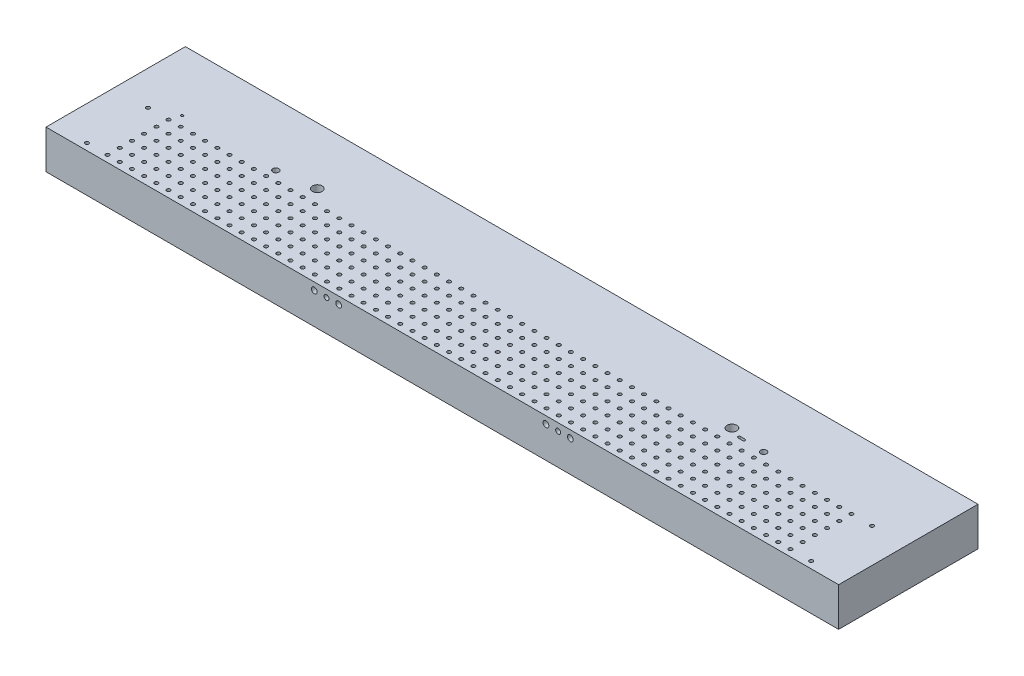
SolidWorks part; units mm, degrees
ref_plane "Front Plane" through (0, 0, 0) normal (0, 0, 1) x (1, 0, 0)
ref_plane "Top Plane" through (0, 0, 0) normal (0, 1, 0) x (1, 0, 0)
ref_plane "Right Plane" through (0, 0, 0) normal (1, 0, 0) x (0, 0, -1)
sketch "Sketch1" plane through (0, 0, 0) normal (0, 1, 0) x (1, 0, 0)
  line L1 (-55.7213, 28.6477) -> (594.2787, 28.6477)
  line L2 (-55.7213, 28.6477) -> (-55.7213, -85.6523)
  line L3 (-55.7213, -85.6523) -> (594.2787, -85.6523)
  line L4 (594.2787, 28.6477) -> (594.2787, -85.6523)
  dimension "D1" = 650
  dimension "D2" = 114.3
extrude "Boss-Extrude1" add sketch "Sketch1" against normal blind 31.75
hole_wizard "Hole2" positions "Sketch5" profile "Sketch4" legacy
sketch "Sketch5" plane through (0, 0, 0) normal (0, 1, 0) x (1, 0, 0)
  line L0 (-55.7213, 28.6477) -> (-55.7213, -85.6523) construction
  line L1 (-55.7213, -85.6523) -> (594.2787, -85.6523) construction
  point P0 (99.2787, -18.1523)
  point P2 (439.2787, -18.1523)
  dimension "D1" = 155
  dimension "D2" = 340
  dimension "D3" = 67.5
  dimension "D4" = 67.5
sketch "Sketch4" plane through (99.2787, 0, 18.1523) normal (1, 0, 0) x (0, 0, 1)
  line L0 (0, 0) -> (0, 15.875)
  line L1 (0, 15.875) -> (3.9815, 15.875)
  line L2 (3.9815, 15.875) -> (3.9815, 0)
  line L3 (3.9815, 0) -> (0, 0)
  line L4 (0, 110) -> (0, -10) construction
  dimension "Diameter" = 7.9629
  dimension "Depth" = 15.875
hole_wizard "Hole3" positions "Sketch10" profile "Sketch9" legacy
sketch "Sketch10" plane through (0, 0, 0) normal (0, 1, 0) x (1, 0, 0)
  line L0 (-55.7213, 28.6477) -> (-55.7213, -85.6523) construction
  point P0 (269.2787, -12.7509)
  dimension "D1" = 325
sketch "Sketch9" plane through (269.2787, 0, 12.7509) normal (1, 0, 0) x (0, 0, 1)
  line L0 (0, 0) -> (0, 15.875)
  line L1 (0, 15.875) -> (3.9815, 15.875)
  line L2 (3.9815, 15.875) -> (3.9815, 0)
  line L3 (3.9815, 0) -> (0, 0)
  line L4 (0, 110) -> (0, -10) construction
  dimension "Diameter" = 7.9629
  dimension "Depth" = 15.875
hole_wizard "Hole4" positions "Sketch12" profile "Sketch11" legacy
sketch "Sketch12" plane through (0, 0, 0) normal (0, 1, 0) x (1, 0, 0)
  line L0 (-55.7213, -85.6523) -> (594.2787, -85.6523) construction
  circle A0 centre (269.2787, -12.7509) radius 3.9814 construction
  point P0 (69.2787, -22.1523)
  point P2 (469.2787, -22.1523)
  dimension "D1" = 200
  dimension "D2" = 200
  dimension "D3" = 63.5
  dimension "D4" = 63.5
sketch "Sketch11" plane through (69.2787, 0, 22.1523) normal (1, 0, 0) x (0, 0, 1)
  line L0 (0, 0) -> (0, 15.875)
  line L1 (0, 15.875) -> (2.5, 15.875)
  line L2 (2.5, 15.875) -> (2.5, 0)
  line L3 (2.5, 0) -> (0, 0)
  line L4 (0, 110) -> (0, -10) construction
  dimension "Diameter" = 5
  dimension "Depth" = 15.875
hole_wizard "Hole6" positions "Sketch16" profile "Sketch15" legacy
sketch "Sketch16" plane through (0, 0, 0) normal (0, 1, 0) x (1, 0, 0)
  line L1 (-55.7213, -85.6523) -> (594.2787, -85.6523) construction
  line L4 (269.2787, 63.6941) -> (269.2787, -120.2188) construction
  point P0 (-27.6213, -30.1523)
  point P2 (-27.6213, -80.1523)
  point P6 (566.1787, -30.1523)
  point P36 (566.1787, -80.1523)
  dimension "D1" = 593.8
  dimension "D2" = 296.9
  dimension "D3" = 296.9
  dimension "D4" = 5.5
  dimension "D6" = 5.5
  dimension "D7" = 50
sketch "Sketch15" plane through (-27.6213, 0, 30.1523) normal (1, 0, 0) x (0, 0, 1)
  line L0 (0, 0) -> (0, 5)
  line L1 (0, 5) -> (1.5, 5)
  line L2 (1.5, 5) -> (1.5, 0)
  line L3 (1.5, 0) -> (0, 0)
  line L4 (0, 110) -> (0, -10) construction
  dimension "Diameter" = 3
  dimension "Depth" = 5
hole_wizard "Hole7" positions "Sketch18" profile "Sketch17" legacy
sketch "Sketch18" plane through (0, 0, 0) normal (0, 1, 0) x (1, 0, 0)
  line L0 (-55.7213, -85.6523) -> (594.2787, -85.6523) construction
  circle A0 centre (269.2787, -12.7509) radius 3.9814 construction
  point P0 (279.2787, -80.1523)
  dimension "D2" = 10
  dimension "D1" = 5.5
sketch "Sketch17" plane through (279.2787, 0, 80.1523) normal (1, 0, 0) x (0, 0, 1)
  line L0 (0, 0) -> (0, 30)
  line L1 (0, 30) -> (1.5, 30)
  line L2 (1.5, 30) -> (1.5, 0)
  line L3 (1.5, 0) -> (0, 0)
  line L4 (0, 110) -> (0, -10) construction
  dimension "Diameter" = 3
  dimension "Depth" = 30
sketch "Sketch19" plane through (0, 0, 0) normal (0, 1, 0) x (1, 0, 0)
  line L0 (277.7787, -80.1523) -> (50277.7787, -80.1523) construction
  line L1 (279.2787, -80.1523) -> (279.2787, 49919.8477) construction
  line L2 (269.2787, 97.4934) -> (269.2787, -133.194) construction
  circle A0 centre (279.2787, -80.1523) radius 1.5 construction
  dimension "D1" = 10
pattern_linear "LPattern2" count 28 spacing 10 along (1, 0, 0) count 6 spacing 10 along (0, 0, -1) of "Hole7"
hole_wizard "Hole12" positions "Sketch34" profile "Sketch33" legacy
sketch "Sketch34" plane through (0, 0, 0) normal (0, 1, 0) x (1, 0, 0)
  line L0 (-199722.2213, -80.1523) -> (250277.7787, -80.1523) construction
  line L1 (269.2787, 97.4934) -> (269.2787, -133.194) construction
  point P0 (269.2787, -80.1523)
sketch "Sketch33" plane through (269.2787, 0, 80.1523) normal (1, 0, 0) x (0, 0, 1)
  line L0 (0, 0) -> (0, 30)
  line L1 (0, 30) -> (1.5, 30)
  line L2 (1.5, 30) -> (1.5, 0)
  line L3 (1.5, 0) -> (0, 0)
  line L4 (0, 110) -> (0, -10) construction
  dimension "Diameter" = 3
  dimension "Depth" = 30
pattern_linear "LPattern3" count 29 spacing 10 along (-1, 0, 0) count 6 spacing 10 along (0, 0, -1) of "Hole12"
sketch "Sketch35" plane through (0, 0, 85.6523) normal (0, 0, 1) x (1, 0, 0)
  line L0 (269.2787, 71.714) -> (269.2787, -64.9274) construction
  line L1 (-55.7213, -31.75) -> (-55.7213, 0) construction
  dimension "D1" = 325
hole_wizard "Hole13" positions "Sketch37" profile "Sketch36" legacy
sketch "Sketch37" plane through (0, 0, 85.6523) normal (0, 0, 1) x (1, 0, 0)
  line L0 (269.2787, 71.714) -> (269.2787, -64.9274) construction
  line L1 (-199722.2213, 0) -> (250277.7787, 0) construction
  point P0 (184.2787, -6)
  point P2 (164.2787, -6)
  point P4 (374.2787, -6)
  point P6 (354.2787, -6)
  dimension "D1" = 105
  dimension "D2" = 85
  dimension "D3" = 105
  dimension "D4" = 85
  dimension "D5" = 6
  dimension "D6" = 6
  dimension "D7" = 6
  dimension "D8" = 6
sketch "Sketch36" plane through (184.2787, -6, 85.6523) normal (1, 0, 0) x (0, -1, 0)
  line L0 (0, 0) -> (0, 12)
  line L1 (0, 12) -> (2.3813, 12)
  line L2 (2.3813, 12) -> (2.3813, 0)
  line L3 (2.3813, 0) -> (0, 0)
  line L4 (0, 110) -> (0, -10) construction
  dimension "Diameter" = 4.7625
  dimension "Depth" = 12
hole_wizard "#10-32 Tapped Hole1" positions "Sketch40" profile "Sketch38" tap size "#10-32" standard "ANSI Inch"
sketch "Sketch40" plane through (0, 0, 85.6523) normal (0, 0, 1) x (1, 0, 0)
  line L0 (269.2787, 71.714) -> (269.2787, -64.9274) construction
  line L1 (-199722.2213, 0) -> (250277.7787, 0) construction
  point P0 (174.2787, -6)
  point P2 (364.2787, -6)
  dimension "D1" = 95
  dimension "D2" = 95
  dimension "D3" = 6
  dimension "D4" = 6
sketch "Sketch38" plane through (174.2787, -6, 85.6523) normal (1, 0, 0) x (0, -1, 0)
  line L0 (0, 0) -> (0, 16.4533)
  line L1 (0, 16.4533) -> (2.0193, 15.24)
  line L2 (2.0193, 15.24) -> (2.0193, 0)
  line L5 (2.0193, 0) -> (0, 0)
  line L10 (0, 16.4533) -> (-2.0193, 15.24) construction
  line L11 (0, -6.35) -> (0, 107.95) construction
  dimension "Tap Drill Dia." = 4.0386
  dimension "Tap Drill Depth" = 15.24
  dimension "Drill Angle" = 118
cosmetic thread "Hole Thread1" parameters "D1"=12.7, "D2"=4.826
cosmetic thread "Hole Thread2" parameters "D1"=12.7, "D2"=4.826
sketch "Sketch41" plane through (0, -31.75, 0) normal (0, -1, 0) x (1, 0, 0)
  line L1 (-15.7213, 81.1523) -> (554.2787, 81.1523)
  line L2 (-15.7213, 81.1523) -> (-15.7213, 26.1523)
  line L3 (-15.7213, 26.1523) -> (554.2787, 26.1523)
  line L4 (554.2787, 81.1523) -> (554.2787, 26.1523)
  line L5 (-55.7213, 85.6523) -> (594.2787, 85.6523) construction
  line L6 (-55.7213, -28.6477) -> (-55.7213, 85.6523) construction
  line L7 (594.2787, 85.6523) -> (594.2787, -28.6477) construction
  dimension "D1" = 4.5
  dimension "D2" = 55
  dimension "D3" = 40
  dimension "D4" = 40
extrude "Cut-Extrude1" cut sketch "Sketch41" against normal blind 8
sketch "Sketch44" plane through (0, -31.75, 0) normal (0, -1, 0) x (1, 0, 0)
  line L0 (554.2787, 81.1523) -> (-15.7213, 81.1523) construction
  line L1 (-18.7213, 84.1523) -> (557.2787, 84.1523)
  line L2 (-18.7213, 84.1523) -> (-18.7213, 23.1523)
  line L3 (-18.7213, 23.1523) -> (557.2787, 23.1523)
  line L4 (557.2787, 84.1523) -> (557.2787, 23.1523)
  line L5 (-15.7213, 26.1523) -> (554.2787, 26.1523) construction
  line L6 (-15.7213, 81.1523) -> (-15.7213, 26.1523) construction
  line L7 (554.2787, 26.1523) -> (554.2787, 81.1523) construction
  dimension "D1" = 3
  dimension "D2" = 3
  dimension "D3" = 3
  dimension "D4" = 3
extrude "Cut-Extrude2" cut sketch "Sketch44" against normal blind 3.2
fillet "Fillet120" radius 3 8 edges at (-18.7213, -30.15, 23.1523) (-15.7213, -26.15, 26.1523) (557.2787, -30.15, 23.1523) (554.2787, -26.15, 26.1523) (554.2787, -26.15, 81.1523) (557.2787, -30.15, 84.1523) (-18.7213, -30.15, 84.1523) (-15.7213, -26.15, 81.1523)
hole_wizard "1/4 NPT Tapped Hole1" positions "Sketch50" profile "Sketch49" size "1/4" standard "ANSI Inch"
sketch "Sketch50" plane through (-55.7213, 0, 0) normal (-1, 0, 0) x (0, 0, 1)
  line L0 (-28.6477, -31.75) -> (85.6523, -31.75) construction
  line L1 (85.6523, -31.75) -> (85.6523, 0) construction
  point P0 (55.1523, -21.25)
  dimension "D1" = 10.5
  dimension "D2" = 30.5
sketch "Sketch49" plane through (-55.7213, -21.25, 55.1523) normal (0, 1, 0) x (0, 0, 1)
  line L0 (0, 0) -> (0, 50.4123)
  line L1 (5.5626, 47.07) -> (0, 50.4123)
  line L2 (-5.5626, 47.07) -> (0, 50.4123) construction
  line L3 (5.5626, 47.07) -> (5.5626, 10.02)
  line L4 (5.5626, 10.02) -> (6.5909, 10.02)
  line L5 (6.5909, 10.02) -> (6.858, 1.0999)
  line L6 (6.858, 1.0999) -> (7.493, 0)
  line L7 (7.493, 0) -> (0, 0)
  line L8 (0, -6.35) -> (0, 107.95) construction
  line L9 (-6.858, 1.0999) -> (-7.493, 0) construction
  line L11 (-5.5626, 10.02) -> (-6.5909, 10.02) construction
  line L12 (-6.5909, 10.02) -> (-6.858, 1.0999) construction
  dimension "Tap Drill Dia." = 11.1252
  dimension "Tap Drill Depth" = 47.07
  dimension "Thread Dia." = 13.716
  dimension "Thread Angle" = 3.43
  dimension "Thread Depth" = 10.02
  dimension "C'Sink Dia." = 14.986
  dimension "C'Sink Angle" = 60
  dimension "Drill Angle" = 118
sketch "Sketch51" plane through (0, 0, 0) normal (0, 1, 0) x (1, 0, 0)
  circle A0 centre (269.2787, -12.7509) radius 3.9814 construction
  circle A1 centre (269.2787, -12.7509) radius 3.9815
extrude "fill hole 3" add sketch "Sketch51" against normal up to next
sketch "Sketch52" plane through (0, 0, 0) normal (0, 1, 0) x (1, 0, 0)
  line L0 (-55.7213, -85.6523) -> (594.2787, -85.6523) construction
  line L1 (269.2787, 97.4934) -> (269.2787, -133.194) construction
  line L2 (448.6787, -21.6523) -> (452.6787, -21.6523) construction
  line L3 (448.6787, -20.6523) -> (452.6787, -20.6523)
  line L4 (448.6787, -22.6523) -> (452.6787, -22.6523)
  circle A0 centre (-8.1213, -21.6523) radius 1
  arc A1 (448.6787, -20.6523) -> (448.6787, -22.6523) centre (448.6787, -21.6523) ccw
  arc A2 (452.6787, -22.6523) -> (452.6787, -20.6523) centre (452.6787, -21.6523) ccw
  point P8 (450.6787, -21.6523)
  dimension "D1" = 64
  dimension "D2" = 277.4
  dimension "D3" = 181.4
extrude "Cut-Extrude3" cut sketch "Sketch52" against normal blind 5
